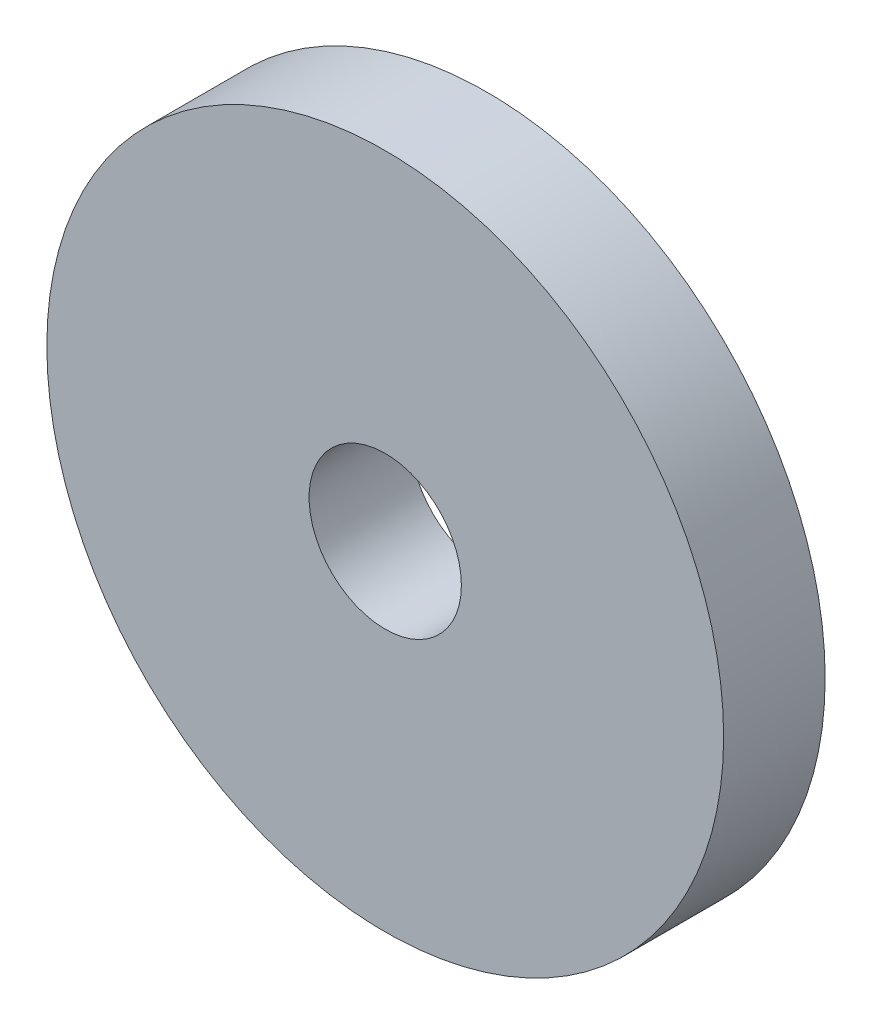
SolidWorks part; units mm, degrees
ref_plane "Front Plane" through (0, 0, 0) normal (0, 0, 1) x (1, 0, 0)
ref_plane "Top Plane" through (0, 0, 0) normal (0, 1, 0) x (1, 0, 0)
ref_plane "Right Plane" through (0, 0, 0) normal (1, 0, 0) x (0, 0, -1)
sketch "Sketch1" plane through (0, 0, 0) normal (0, 0, 1) x (1, 0, 0)
  circle A0 centre (0, 0) radius 10
  circle A1 centre (0, 0) radius 2.25
  dimension "D1" = 20
  dimension "D2" = 4.5
extrude "Boss-Extrude1" add sketch "Sketch1" along normal blind 3
